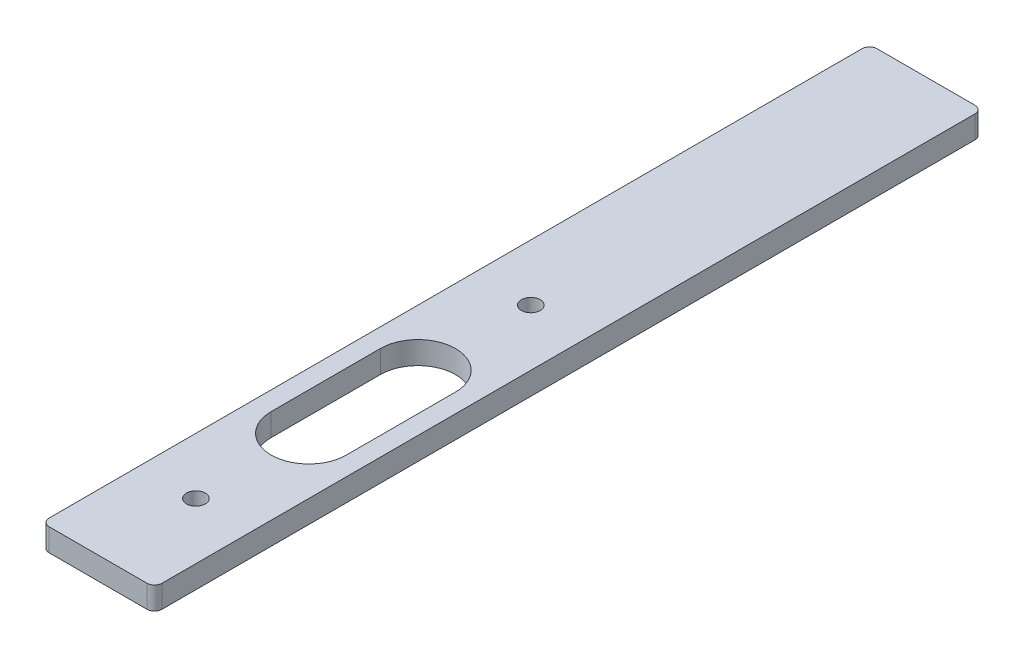
SolidWorks part; units mm, degrees
ref_plane "前视基准面" through (0, 0, 0) normal (0, 0, 1) x (1, 0, 0)
ref_plane "上视基准面" through (0, 0, 0) normal (0, 1, 0) x (1, 0, 0)
ref_plane "右视基准面" through (0, 0, 0) normal (1, 0, 0) x (0, 0, -1)
other "Configuration Table"
sketch "草图1" plane through (0, 0, 0) normal (0, 1, 0) x (1, 0, 0)
  line L1 (0, 0) -> (15, 0)
  line L2 (0, 0) -> (0, 110)
  line L3 (0, 110) -> (15, 110)
  line L4 (15, 0) -> (15, 110)
  dimension "D1" = 15
  dimension "D2" = 110
extrude "凸台-拉伸1" add sketch "草图1" along normal blind 3
fillet "圆角1" radius 1 4 edges at (15, 1.5, -110) (0, 1.5, -110) (15, 1.5, 0) (0, 1.5, 0)
sketch "草图2" plane through (0, 3, 0) normal (0, 1, 0) x (1, 0, 0)
  line L0 (7.5, 0) -> (7.5, 110) construction
  line L1 (1, 0) -> (14, 0) construction
  line L2 (14, 110) -> (1, 110) construction
  circle A0 centre (7.5, 13) radius 1.25
  circle A1 centre (7.5, 57.5) radius 1.25
  dimension "D2" = 2.5
  dimension "D3" = 2.5
  dimension "D1" = 13
  dimension "D4" = 44.5
extrude "切除-拉伸1" cut sketch "草图2" against normal blind 3
sketch "草图3" plane through (0, 3, 0) normal (0, 1, 0) x (1, 0, 0)
  line L0 (7.5, 57.5) -> (7.5, 13) construction
  line L1 (7.5, 42.5) -> (7.5, 28) construction
  line L2 (12.5, 42.5) -> (12.5, 28)
  line L3 (2.5, 42.5) -> (2.5, 28)
  arc A0 (12.5, 42.5) -> (2.5, 42.5) centre (7.5, 42.5) ccw
  arc A1 (2.5, 28) -> (12.5, 28) centre (7.5, 28) ccw
  point P6 (7.5, 35.25)
  dimension "D3" = 5
  dimension "D1" = 15
  dimension "D2" = 15
extrude "切除-拉伸2" cut sketch "草图3" against normal blind 10
